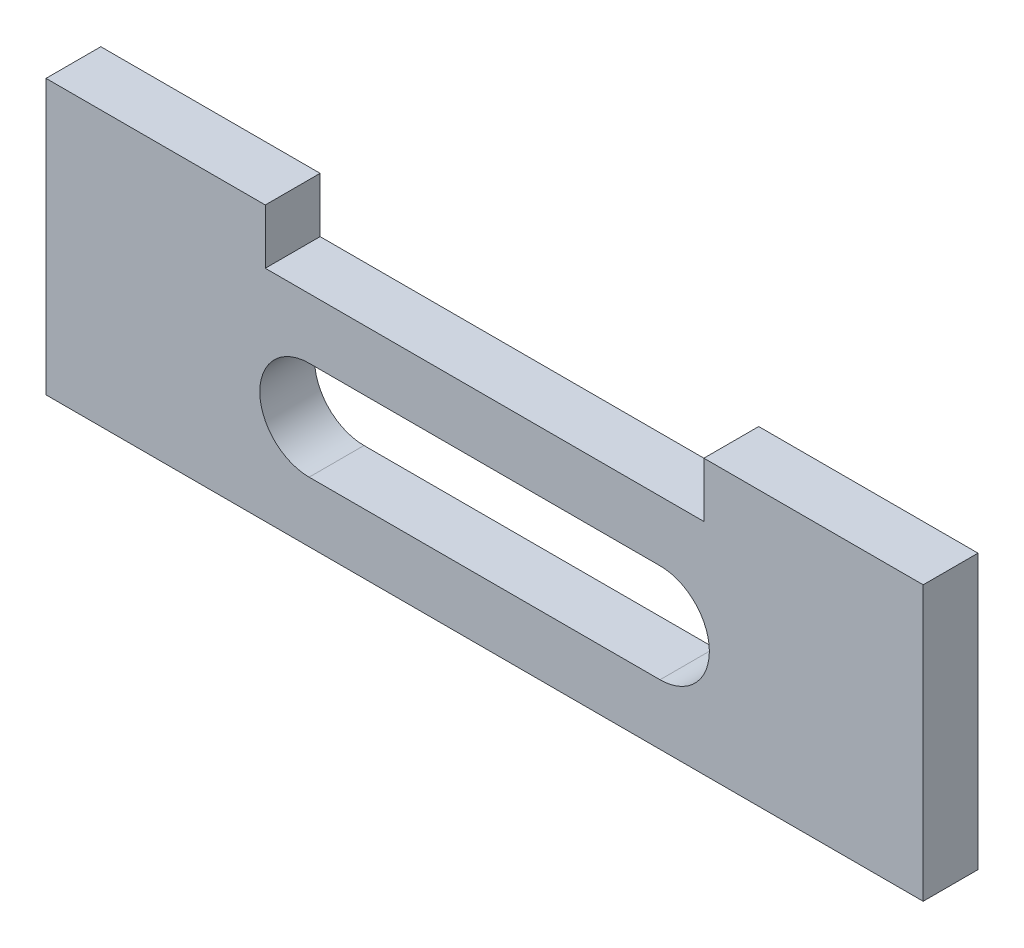
SolidWorks part; units mm, degrees
ref_plane "Front Plane" through (0, 0, 0) normal (0, 0, 1) x (1, 0, 0)
ref_plane "Top Plane" through (0, 0, 0) normal (0, 1, 0) x (1, 0, 0)
ref_plane "Right Plane" through (0, 0, 0) normal (1, 0, 0) x (0, 0, -1)
sketch "Sketch1" plane through (0, 0, 0) normal (0, 0, 1) x (1, 0, 0)
  line L1 (0, 0) -> (50.8, 0)
  line L2 (0, 0) -> (0, 12.7)
  line L3 (0, 12.7) -> (50.8, 12.7)
  line L4 (50.8, 0) -> (50.8, 12.7)
  dimension "D1" = 50.8
  dimension "D2" = 12.7
extrude "Extrude1" add sketch "Sketch1" along normal blind 3.175
sketch "Sketch2" plane through (0, 0, 3.175) normal (0, 0, 1) x (1, 0, 0)
  line L0 (15.24, 6.35) -> (35.56, 6.35) construction
  line L1 (15.24, 9.2075) -> (35.56, 9.2075)
  line L2 (15.24, 3.4925) -> (35.56, 3.4925)
  line L3 (50.8, 0) -> (50.8, 12.7) construction
  line L4 (0, 0) -> (50.8, 0) construction
  arc A0 (15.24, 9.2075) -> (15.24, 3.4925) centre (15.24, 6.35) ccw
  arc A1 (35.56, 3.4925) -> (35.56, 9.2075) centre (35.56, 6.35) ccw
  point P2 (25.4, 6.35)
  dimension "D1" = 5.715
  dimension "D2" = 25.4
  dimension "D3" = 20.32
  dimension "D4" = 6.35
extrude "Extrude2" cut sketch "Sketch2" against normal through all
sketch "Sketch3" plane through (0, 12.7, 0) normal (0, 1, 0) x (1, 0, 0)
  line L0 (50.8, -3.175) -> (0, -3.175) construction
  line L1 (0, 0) -> (12.7, 0)
  line L2 (0, 0) -> (0, -3.175)
  line L3 (0, -3.175) -> (12.7, -3.175)
  line L4 (12.7, 0) -> (12.7, -3.175)
  dimension "D1" = 3.175
  dimension "D2" = 12.7
extrude "Extrude3" add sketch "Sketch3" along normal blind 3.175
pattern_linear "LPattern1" count 2 spacing 38.1 along (1, 0, 0) of "Extrude3"
